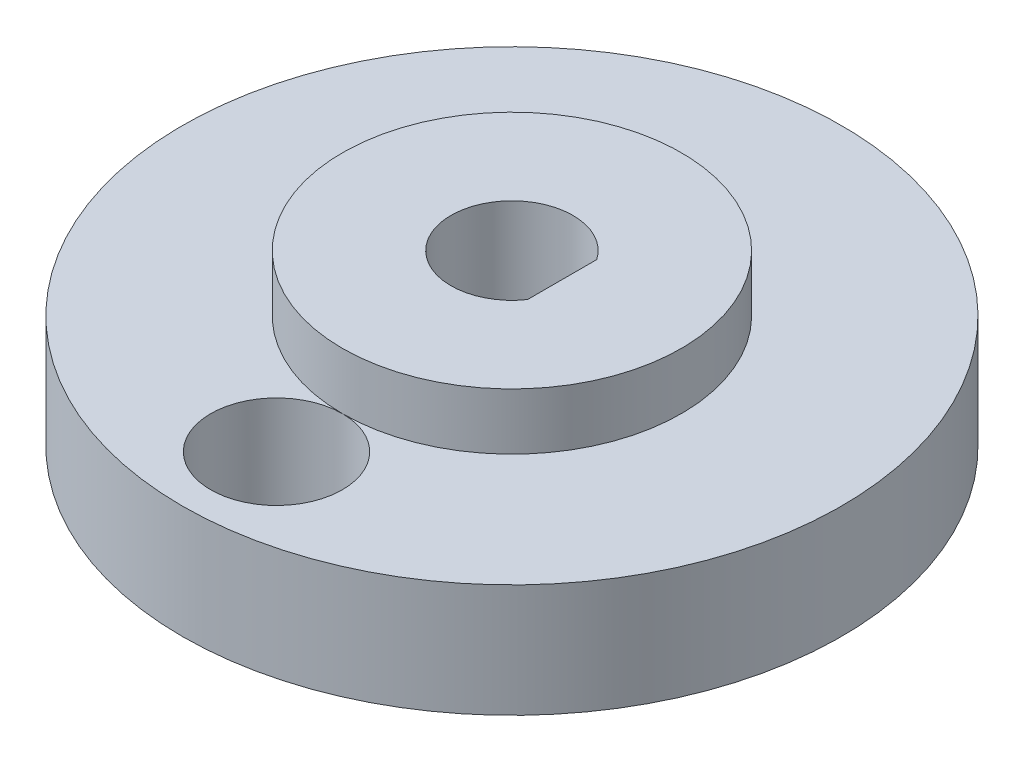
SolidWorks part; units mm, degrees
ref_plane "Front Plane" through (0, 0, 0) normal (0, 0, 1) x (1, 0, 0)
ref_plane "Top Plane" through (0, 0, 0) normal (0, 1, 0) x (1, 0, 0)
ref_plane "Right Plane" through (0, 0, 0) normal (1, 0, 0) x (0, 0, -1)
sketch "Sketch1" plane through (0, 0, 0) normal (0, 1, 0) x (1, 0, 0)
  circle A0 centre (0, 0) radius 17.5
  dimension "D1" = 35
extrude "Boss-Extrude1" add sketch "Sketch1" along normal blind 6
sketch "Sketch3" plane through (0, 6, 0) normal (0, 1, 0) x (1, 0, 0)
  circle A0 centre (0, 0) radius 9
  dimension "D1" = 18
extrude "Boss-Extrude2" add sketch "Sketch3" along normal blind 3
sketch "Sketch4" plane through (0, 9, 0) normal (0, 1, 0) x (1, 0, 0)
  line L0 (0, 0) -> (2.667, 0) construction
  line L1 (2.667, 3.5) -> (2.667, -3.5)
  circle A0 centre (0, 0) radius 3.2385
  point P6 (0, 0)
  point P7 (0, 0)
  dimension "D1" = 6.477
  dimension "D2" = 2.667
  dimension "D3" = 7
  dimension "D4" = 3.5
extrude "Cut-Extrude1" cut sketch "Sketch4" against normal through all
sketch "Sketch5" plane through (0, 0, 0) normal (0, 1, 0) x (1, 0, 0)
  line L0 (0, 0) -> (0, -12.5) construction
  circle A0 centre (0, -12.5) radius 3.5
  dimension "D1" = 7
  dimension "D2" = 12.5
extrude "Cut-Extrude2" cut sketch "Sketch5" along normal through all
